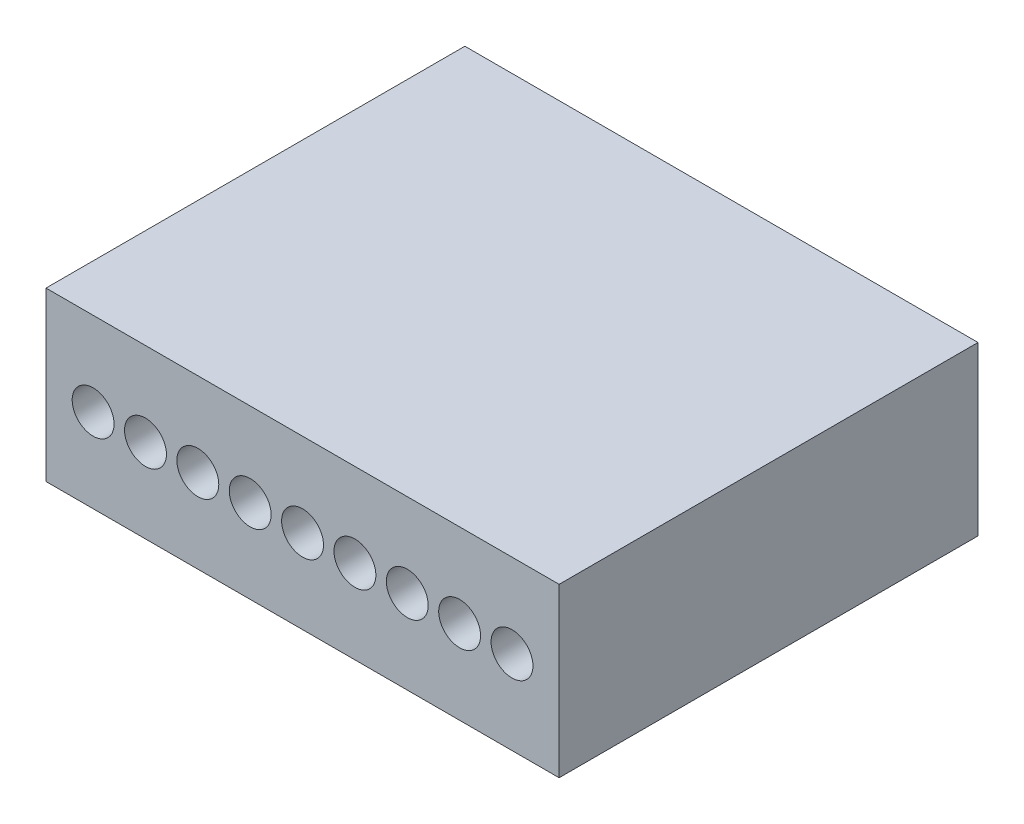
SolidWorks part; units mm, degrees
ref_plane "Front Plane" through (0, 0, 0) normal (0, 0, 1) x (1, 0, 0)
ref_plane "Top Plane" through (0, 0, 0) normal (0, 1, 0) x (1, 0, 0)
ref_plane "Right Plane" through (0, 0, 0) normal (1, 0, 0) x (0, 0, -1)
sketch "Sketch2" plane through (0, 0, 0) normal (0, 0, 1) x (1, 0, 0)
  line L1 (0, 0) -> (12.25, 0)
  line L2 (0, 0) -> (0, 4)
  line L3 (0, 4) -> (12.25, 4)
  line L4 (12.25, 0) -> (12.25, 4)
  dimension "D1" = 12.25
  dimension "D2" = 4
extrude "Boss-Extrude1" add sketch "Sketch2" along normal blind 10
sketch "Sketch3" plane through (0, 0, 10) normal (0, 0, 1) x (1, 0, 0)
  line L0 (0, 2) -> (12.25, 2) construction
  line L1 (0, 4) -> (0, 0) construction
  line L2 (12.25, 0) -> (12.25, 4) construction
  line L3 (0, 2) -> (12.25, 2) construction
  line L4 (12.25, 4) -> (0, 4) construction
  line L5 (0, 0) -> (12.25, 0) construction
  line L6 (1.125, 4) -> (1.125, 0) construction
  circle A0 centre (1.125, 2) radius 0.5
  circle A1 centre (2.375, 2) radius 0.5
  circle A2 centre (3.625, 2) radius 0.5
  circle A3 centre (4.875, 2) radius 0.5
  circle A4 centre (6.125, 2) radius 0.5
  circle A5 centre (7.375, 2) radius 0.5
  circle A6 centre (8.625, 2) radius 0.5
  circle A7 centre (9.875, 2) radius 0.5
  circle A8 centre (11.125, 2) radius 0.5
  circle A21 centre (24.875, 2) radius 0.5 [skipped]
  circle A22 centre (23.625, 2) radius 0.5 [skipped]
  circle A23 centre (22.375, 2) radius 0.5 [skipped]
  circle A24 centre (21.125, 2) radius 0.5 [skipped]
  circle A25 centre (19.875, 2) radius 0.5 [skipped]
  circle A26 centre (18.625, 2) radius 0.5 [skipped]
  circle A27 centre (17.375, 2) radius 0.5 [skipped]
  circle A28 centre (16.125, 2) radius 0.5 [skipped]
  circle A29 centre (14.875, 2) radius 0.5 [skipped]
  circle A30 centre (13.625, 2) radius 0.5 [skipped]
  circle A31 centre (12.375, 2) radius 0.5 [skipped]
  dimension "D1" = 1
  dimension "D2" = 2
  dimension "D3" = 1.125
  dimension "D5" = 1.25
  dimension "D4" = 20
extrude "Cut-Extrude1" cut sketch "Sketch3" against normal blind 5
sketch "Sketch4" plane through (0, 0, 10) normal (0, 0, 1) x (1, 0, 0)
  point P0 (1.125, 2)
  point P1 (2.375, 2)
  point P3 (3.625, 2)
  point P5 (4.875, 2)
  point P7 (6.125, 2)
  point P9 (7.375, 2)
  point P11 (8.625, 2)
  point P13 (9.875, 2)
  point P15 (11.125, 2)
  point P27 (0, 0)
  point P37 (0, 0)
